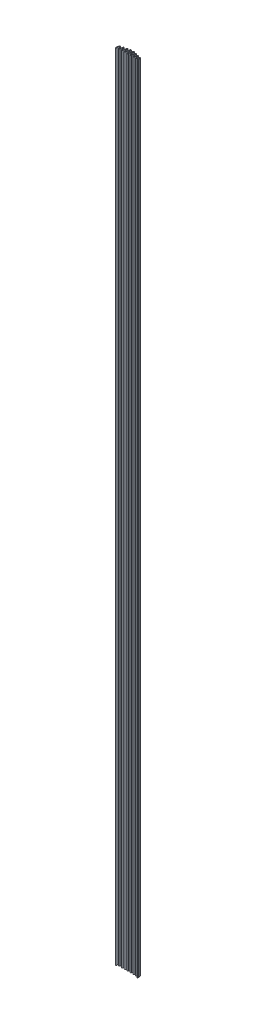
SolidWorks part; units mm, degrees
material "6463-T6"
ref_plane "Front Plane" through (0, 0, 0) normal (0, 0, 1) x (1, 0, 0)
ref_plane "Top Plane" through (0, 0, 0) normal (0, 1, 0) x (1, 0, 0)
ref_plane "Right Plane" through (0, 0, 0) normal (1, 0, 0) x (0, 0, -1)
sketch "Sketch1" plane through (0, 0, 0) normal (0, 1, 0) x (1, 0, 0)
  line L0 (0, 0) -> (101.6, 0) construction
  line L1 (0, 0) -> (0, 19.05) construction
  line L2 (0, 19.05) -> (101.6, 19.05) construction
  line L3 (101.6, 19.05) -> (101.6, 0) construction
  line L4 (0, 6.35) -> (101.6, 6.35) construction
  line L5 (0, 8.89) -> (101.6, 8.89) construction
  line L6 (0, 12.7) -> (101.6, 12.7) construction
  line L7 (0, 16.51) -> (101.6, 16.51) construction
  line L8 (6.35, 0) -> (6.35, 19.05) construction
  line L9 (12.7, 0) -> (12.7, 19.05) construction
  line L10 (19.05, 0) -> (19.05, 19.05) construction
  line L11 (25.4, 0) -> (25.4, 19.05) construction
  line L12 (31.75, 0) -> (31.75, 19.05) construction
  line L13 (38.1, 0) -> (38.1, 19.05) construction
  line L14 (44.45, 0) -> (44.45, 19.05) construction
  line L15 (50.8, 0) -> (50.8, 19.05) construction
  line L16 (57.15, 0) -> (57.15, 19.05) construction
  line L17 (63.5, 0) -> (63.5, 19.05) construction
  line L18 (69.85, 0) -> (69.85, 19.05) construction
  line L19 (76.2, 0) -> (76.2, 19.05) construction
  line L20 (82.55, 0) -> (82.55, 19.05) construction
  line L21 (88.9, 0) -> (88.9, 19.05) construction
  line L22 (95.25, 0) -> (95.25, 19.05) construction
  line L23 (0, 1.6002) -> (101.6, 1.6002) construction
  line L24 (0, 3.2004) -> (101.6, 3.2004) construction
  line L25 (1.5405, 1.1671) -> (3.9048, 9.5774)
  line L26 (11.1595, 1.1671) -> (8.7952, 9.5774)
  line L27 (16.5557, 13.1795) -> (14.2714, 1.2981)
  line L28 (23.8286, 1.2981) -> (21.5443, 13.1795)
  line L29 (26.9836, 1.3701) -> (29.2364, 16.8752)
  line L30 (36.5164, 1.3701) -> (34.2636, 16.8752)
  line L31 (39.6879, 1.402) -> (41.9296, 19.3645)
  line L32 (49.2121, 1.402) -> (46.9704, 19.3645)
  line L33 (52.3879, 1.402) -> (54.6296, 19.3645)
  line L34 (61.9121, 1.402) -> (59.6704, 19.3645)
  line L35 (65.0836, 1.3701) -> (67.3364, 16.8752)
  line L36 (74.6164, 1.3701) -> (72.3636, 16.8752)
  line L37 (77.7714, 1.2981) -> (80.0557, 13.1795)
  line L38 (87.3286, 1.2981) -> (85.0443, 13.1795)
  line L39 (90.4405, 1.1671) -> (92.8048, 9.5774)
  line L40 (100.0595, 1.1671) -> (97.6952, 9.5774)
  line L41 (3.0076, 0.7547) -> (5.3719, 9.165)
  line L42 (9.6924, 0.7547) -> (7.3281, 9.165)
  line L43 (18.0523, 12.8918) -> (15.768, 1.0104)
  line L44 (22.332, 1.0104) -> (20.0477, 12.8918)
  line L45 (28.4917, 1.151) -> (30.7446, 16.6561)
  line L46 (35.0083, 1.151) -> (32.7554, 16.6561)
  line L47 (41.2002, 1.2133) -> (43.4418, 19.1758)
  line L48 (47.6998, 1.2133) -> (45.4582, 19.1758)
  line L49 (53.9002, 1.2133) -> (56.1418, 19.1758)
  line L50 (60.3998, 1.2133) -> (58.1582, 19.1758)
  line L51 (66.5917, 1.151) -> (68.8446, 16.6561)
  line L52 (73.1083, 1.151) -> (70.8554, 16.6561)
  line L53 (79.268, 1.0104) -> (81.5523, 12.8918)
  line L54 (85.832, 1.0104) -> (83.5477, 12.8918)
  line L55 (91.9076, 0.7547) -> (94.2719, 9.165)
  line L56 (98.5924, 0.7547) -> (96.2281, 9.165)
  line L57 (0, -1.524) -> (0, 0)
  line L58 (101.6, -1.524) -> (101.6, 0)
  arc A1 (8.7952, 9.5774) -> (3.9048, 9.5774) centre (6.35, 8.89) ccw
  arc A2 (21.5443, 13.1795) -> (16.5557, 13.1795) centre (19.05, 12.7) ccw
  arc A3 (34.2636, 16.8752) -> (29.2364, 16.8752) centre (31.75, 16.51) ccw
  arc A4 (46.9704, 19.3645) -> (41.9296, 19.3645) centre (44.45, 19.05) ccw
  arc A5 (59.6704, 19.3645) -> (54.6296, 19.3645) centre (57.15, 19.05) ccw
  arc A6 (72.3636, 16.8752) -> (67.3364, 16.8752) centre (69.85, 16.51) ccw
  arc A7 (85.0443, 13.1795) -> (80.0557, 13.1795) centre (82.55, 12.7) ccw
  arc A8 (97.6952, 9.5774) -> (92.8048, 9.5774) centre (95.25, 8.89) ccw
  arc A9 (0, 0) -> (1.5405, 1.1671) centre (0, 1.6002) ccw
  arc A10 (11.1595, 1.1671) -> (14.2714, 1.2981) centre (12.7, 1.6002) ccw
  arc A11 (23.8286, 1.2981) -> (26.9836, 1.3701) centre (25.4, 1.6002) ccw
  arc A12 (36.5164, 1.3701) -> (39.6879, 1.402) centre (38.1, 1.6002) ccw
  arc A13 (49.2121, 1.402) -> (52.3879, 1.402) centre (50.8, 1.6002) ccw
  arc A14 (61.9121, 1.402) -> (65.0836, 1.3701) centre (63.5, 1.6002) ccw
  arc A15 (74.6164, 1.3701) -> (77.7714, 1.2981) centre (76.2, 1.6002) ccw
  arc A16 (87.3286, 1.2981) -> (90.4405, 1.1671) centre (88.9, 1.6002) ccw
  arc A17 (100.0595, 1.1671) -> (101.6, 0) centre (101.6, 1.6002) ccw
  arc A18 (0, -1.524) -> (3.0076, 0.7547) centre (0, 1.6002) ccw
  arc A19 (7.3281, 9.165) -> (5.3719, 9.165) centre (6.35, 8.89) ccw
  arc A20 (9.6924, 0.7547) -> (15.768, 1.0104) centre (12.7, 1.6002) ccw
  arc A21 (20.0477, 12.8918) -> (18.0523, 12.8918) centre (19.05, 12.7) ccw
  arc A22 (22.332, 1.0104) -> (28.4917, 1.151) centre (25.4, 1.6002) ccw
  arc A23 (32.7554, 16.6561) -> (30.7446, 16.6561) centre (31.75, 16.51) ccw
  arc A24 (35.0083, 1.151) -> (41.2002, 1.2133) centre (38.1, 1.6002) ccw
  arc A25 (45.4582, 19.1758) -> (43.4418, 19.1758) centre (44.45, 19.05) ccw
  arc A26 (47.6998, 1.2133) -> (53.9002, 1.2133) centre (50.8, 1.6002) ccw
  arc A27 (58.1582, 19.1758) -> (56.1418, 19.1758) centre (57.15, 19.05) ccw
  arc A28 (60.3998, 1.2133) -> (66.5917, 1.151) centre (63.5, 1.6002) ccw
  arc A29 (70.8554, 16.6561) -> (68.8446, 16.6561) centre (69.85, 16.51) ccw
  arc A30 (73.1083, 1.151) -> (79.268, 1.0104) centre (76.2, 1.6002) ccw
  arc A31 (83.5477, 12.8918) -> (81.5523, 12.8918) centre (82.55, 12.7) ccw
  arc A32 (85.832, 1.0104) -> (91.9076, 0.7547) centre (88.9, 1.6002) ccw
  arc A33 (96.2281, 9.165) -> (94.2719, 9.165) centre (95.25, 8.89) ccw
  arc A34 (98.5924, 0.7547) -> (101.6, -1.524) centre (101.6, 1.6002) ccw
other "AlignGroup1"
other "AlignGroup2"
other "AlignGroup3" parameters "D10"=2.4117, "D13"=3.2004, "D1"=86.8219, "D2"=13.2255, "D3"=6.35, "D4"=8.89, "D5"=12.7, "D6"=16.51, "D7"=19.05, "D8"=19.05, "D9"=5.2861, "D11"=101.6, "D12"=101.6, "D14"=1.6002
extrude "Boss-Extrude1" add sketch "Sketch1" against normal blind 3505.2
sketch "Sketch2" plane through (0, 0, 0) normal (0, 1, 0) x (1, 0, 0)
  line L0 (0, -0.762) -> (0, -1.524)
  line L1 (0, 0) -> (0, -1.524) construction
  line L2 (0, -1.524) -> (0.2773, -1.524)
  line L3 (0.2773, -1.524) -> (0, -0.762)
  line L4 (101.6, -0.762) -> (101.6, -1.524)
  line L5 (101.6, -1.524) -> (101.6, 0) construction
  line L6 (101.6, -1.524) -> (101.3227, -1.524)
  line L7 (101.3227, -1.524) -> (101.6, -0.762)
  dimension "D1" = 0.762
  dimension "D2" = 20
  dimension "D3" = 0.762
  dimension "D4" = 20
extrude "Cut-Extrude1" cut sketch "Sketch2" against normal through all
sketch "Sketch3" plane through (0, 0, 0) normal (0, 1, 0) x (1, 0, 0)
  line L0 (50.8, 25.2866) -> (50.8, -7.6819) construction
  line L2 (101.2533, -1.7145) -> (101.327, -1.512)
  line L3 (0.273, -1.512) -> (0, -0.762) construction
  line L4 (1.6375, -5.261) -> (1.411, -4.6388)
  line L5 (2.794, -1.7145) -> (0.3467, -1.7145)
  line L6 (2.794, -4.1275) -> (1.7691, -4.1275)
  line L7 (0.3467, -1.7145) -> (0.273, -1.512)
  line L8 (98.806, -4.1275) -> (99.8309, -4.1275)
  line L9 (98.806, -1.7145) -> (101.2533, -1.7145)
  line L10 (99.9625, -5.261) -> (100.189, -4.6388)
  arc A0 (2.794, -4.1275) -> (2.794, -1.7145) centre (2.794, -2.921) ccw
  arc A3 (1.866, -5.489) -> (3.5115, -0.2865) centre (2.794, -2.921) ccw
  arc A4 (0.273, -1.512) -> (3.0076, 0.7547) centre (0, 1.6002) ccw construction
  arc A5 (1.6375, -5.261) -> (1.866, -5.489) centre (1.9955, -5.1307) ccw
  arc A6 (2.9839, 0.6745) -> (3.5115, -0.2865) centre (3.7117, 0.4488) ccw
  arc A7 (0.273, -1.512) -> (2.9839, 0.6745) centre (0, 1.6002) ccw
  arc A8 (1.411, -4.6388) -> (1.7691, -4.1275) centre (1.7691, -4.5085) cw
  arc A9 (100.189, -4.6388) -> (99.8309, -4.1275) centre (99.8309, -4.5085) ccw
  arc A10 (101.327, -1.512) -> (98.6161, 0.6745) centre (101.6, 1.6002) cw
  arc A11 (98.6161, 0.6745) -> (98.0885, -0.2865) centre (97.8883, 0.4488) cw
  arc A12 (99.9625, -5.261) -> (99.734, -5.489) centre (99.6045, -5.1307) cw
  arc A13 (99.734, -5.489) -> (98.0885, -0.2865) centre (98.806, -2.921) cw
  arc A15 (98.806, -4.1275) -> (98.806, -1.7145) centre (98.806, -2.921) cw
  point P23 (1.6957, -5.4209)
  point P43 (99.9043, -5.4209)
  dimension "D2" = 2.921
  dimension "D4" = 2.413
  dimension "D5" = 2.7305
  dimension "D6" = 0.762
  dimension "D7" = 0.381
  dimension "D1" = 50.8
  dimension "D3" = 2.794
extrude "Boss-Extrude2" add sketch "Sketch3" against normal through all
fillet "Fillet1" radius 0.508 2 edges at (101.2533, -1752.6, 1.7145) (0.3467, -1752.6, 1.7145)
